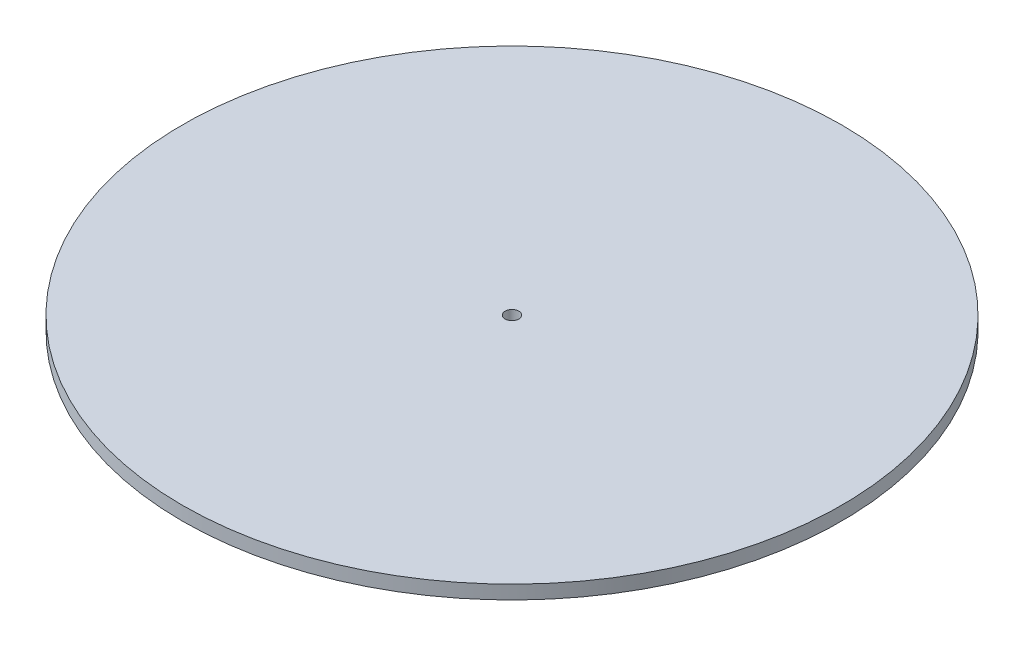
SolidWorks part; units mm, degrees
material "Prop"
ref_plane "Front Plane" through (0, 0, 0) normal (0, 0, 1) x (1, 0, 0)
ref_plane "Top Plane" through (0, 0, 0) normal (0, 1, 0) x (1, 0, 0)
ref_plane "Right Plane" through (0, 0, 0) normal (1, 0, 0) x (0, 0, -1)
sketch "Sketch1" plane through (0, 0, 0) normal (0, 1, 0) x (1, 0, 0)
  circle A0 centre (0, 0) radius 152.4
  circle A1 centre (0, 0) radius 3.175
  dimension "D1" = 6.35
  dimension "D2" = 304.8
extrude "Boss-Extrude1" add sketch "Sketch1" along normal blind 6.35
